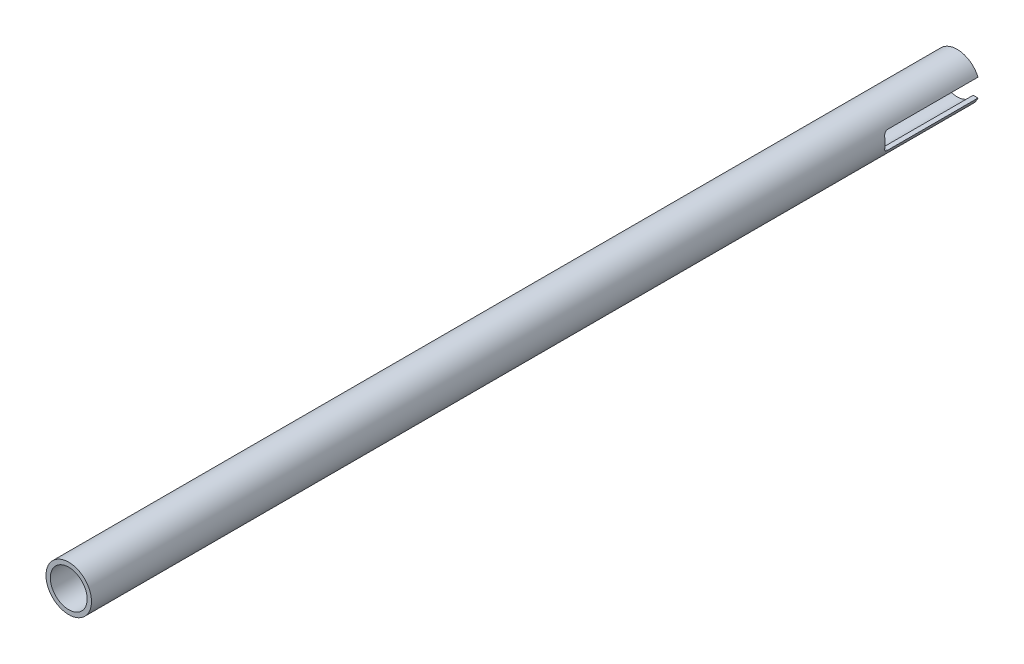
SolidWorks part; units mm, degrees
material "AISI 4130 Steel, annealed at 865C"
ref_plane "Front Plane" through (0, 0, 0) normal (0, 0, 1) x (1, 0, 0)
ref_plane "Top Plane" through (0, 0, 0) normal (0, 1, 0) x (1, 0, 0)
ref_plane "Right Plane" through (0, 0, 0) normal (1, 0, 0) x (0, 0, -1)
sketch "Sketch1" plane through (0, 0, 0) normal (0, 0, 1) x (1, 0, 0)
  circle A0 centre (0, 0) radius 6.477
  circle A1 centre (0, 0) radius 8.001
  dimension "D1" = 12.954
  dimension "D2" = 16.002
extrude "Boss-Extrude1" add sketch "Sketch1" along normal blind 312.42
sketch "Sketch2" plane through (0, 0, 0) normal (1, 0, 0) x (0, 0, -1)
  line L0 (0, 3.175) -> (-31.75, 3.175)
  line L1 (0, 55) -> (0, -55) construction
  line L2 (-31.75, -3.175) -> (0, -3.175)
  line L3 (-33.274, 1.651) -> (-33.274, -1.651)
  line L4 (0, -8.001) -> (0, 8.001) construction
  arc A0 (-33.274, 1.651) -> (-31.75, 3.175) centre (-31.75, 1.651) cw
  arc A1 (-31.75, -3.175) -> (-33.274, -1.651) centre (-31.75, -1.651) cw
  dimension "D5" = 31.75
  dimension "D6" = 33.274
  dimension "D1" = 33.274
  dimension "D2" = 31.75
  dimension "D3" = 6.35
  dimension "D4" = 3.175
extrude "Cut-Extrude2" cut sketch "Sketch2" against normal through all both and the other way through all
